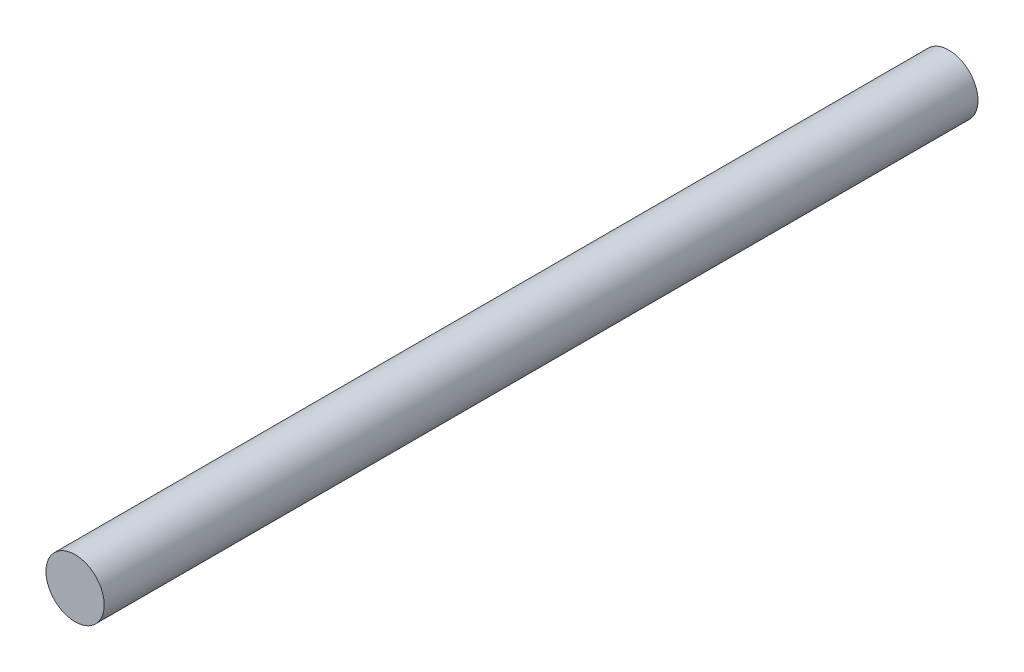
SolidWorks part; units mm, degrees
ref_plane "Спереди" through (0, 0, 0) normal (0, 0, 1) x (1, 0, 0)
ref_plane "Сверху" through (0, 0, 0) normal (0, 1, 0) x (1, 0, 0)
ref_plane "Справа" through (0, 0, 0) normal (1, 0, 0) x (0, 0, -1)
other "Configuration Table"
sketch "Sketch1" plane through (0, 0, 0) normal (0, 0, 1) x (1, 0, 0)
  circle A0 centre (0, 10.6109) radius 1
  dimension "D1" = 2
extrude "Boss-Extrude1" add sketch "Sketch1" along normal blind 30 contours A0
equation "\"R small\"= 2"
equation "\"R big\"= 4"
equation "\"width\"= 0.6"
equation "\"border width\"= 1"
equation "\"D1@Sketch1\"=\"R small\""
